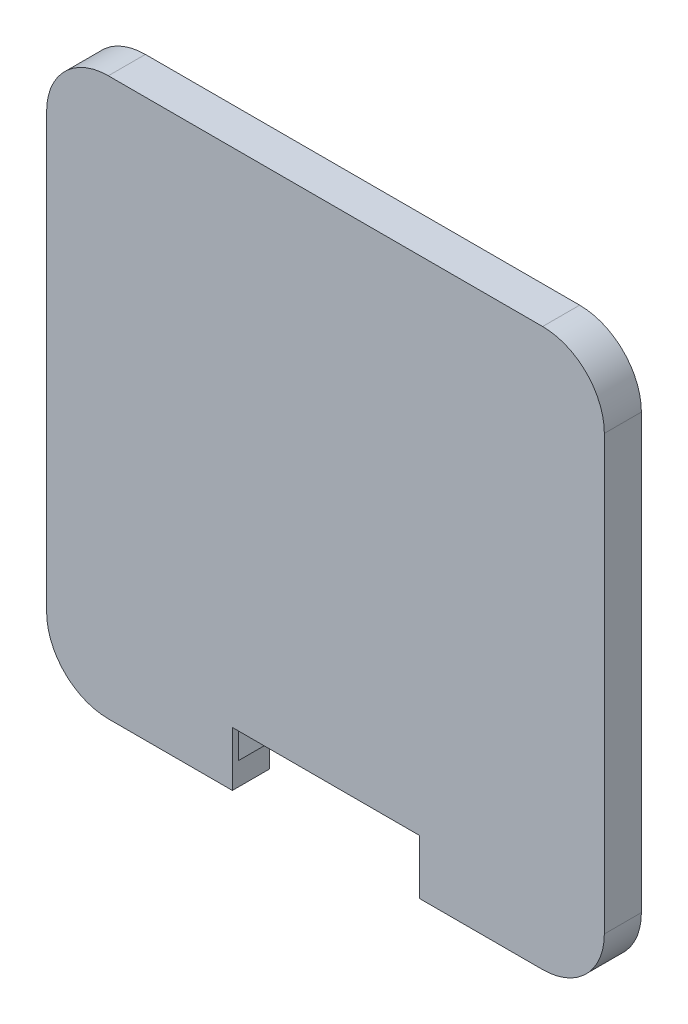
SolidWorks part; units mm, degrees
material "PET"
ref_plane "Front Plane" through (0, 0, 0) normal (0, 0, 1) x (1, 0, 0)
ref_plane "Top Plane" through (0, 0, 0) normal (0, 1, 0) x (1, 0, 0)
ref_plane "Right Plane" through (0, 0, 0) normal (1, 0, 0) x (0, 0, -1)
sketch "Sketch1" plane through (0, 0, 0) normal (0, 0, 1) x (1, 0, 0)
  line L8 (-50.8502, -30.122) -> (-45.1855, -30.122)
  line L9 (15.2147, -41.425) -> (15.2147, -45.122)
  line L10 (-35.1855, -45.122) -> (35.1855, -45.122)
  line L11 (-45.1855, -35.122) -> (-45.1855, 35.122)
  line L12 (-35.1855, 45.122) -> (35.1855, 45.122)
  line L13 (45.1855, -35.122) -> (45.1855, 35.122)
  line L14 (-45.1855, -45.122) -> (45.1855, 45.122) construction
  line L15 (-45.1855, 45.122) -> (45.1855, -45.122) construction
  line L16 (-30.1855, 24.892) -> (-30.1855, -24.892)
  line L17 (-24.9555, -30.122) -> (-19.7221, -30.122)
  line L18 (-19.7221, -30.122) -> (-15.0866, -41.425)
  line L19 (-15.0866, -41.425) -> (15.2147, -41.425)
  line L20 (15.2147, -41.425) -> (19.7232, -30.122)
  line L21 (19.7232, -30.122) -> (24.9555, -30.122)
  line L22 (30.1855, -24.892) -> (30.1855, 24.892)
  line L23 (24.9555, 30.122) -> (-24.9555, 30.122)
  line L24 (-30.1855, 24.892) -> (-30.1855, -24.892)
  line L25 (-24.9555, -30.122) -> (-19.7221, -30.122)
  line L26 (-19.7221, -30.122) -> (-15.0866, -41.425)
  line L27 (-15.0866, -41.425) -> (15.2147, -41.425)
  line L28 (15.2147, -41.425) -> (19.7232, -30.122)
  line L29 (19.7232, -30.122) -> (24.9555, -30.122)
  line L30 (30.1855, -24.892) -> (30.1855, 24.892)
  line L31 (24.9555, 30.122) -> (-24.9555, 30.122)
  line L32 (-15.0866, -41.425) -> (-15.0866, -45.122)
  line L33 (19.7232, -30.122) -> (24.9555, -30.122)
  line L34 (45.1855, -30.122) -> (50.8502, -30.122)
  line L35 (-24.9555, -30.122) -> (-19.7221, -30.122)
  arc A4 (35.1855, -45.122) -> (45.1855, -35.122) centre (35.1855, -35.122) ccw
  arc A5 (-35.1855, -45.122) -> (-45.1855, -35.122) centre (-35.1855, -35.122) cw
  arc A6 (-45.1855, 35.122) -> (-35.1855, 45.122) centre (-35.1855, 35.122) cw
  arc A7 (35.1855, 45.122) -> (45.1855, 35.122) centre (35.1855, 35.122) cw
  arc A8 (-24.9555, 30.122) -> (-30.1855, 24.892) centre (-24.9555, 24.892) ccw
  arc A9 (-30.1855, -24.892) -> (-24.9555, -30.122) centre (-24.9555, -24.892) ccw
  arc A10 (24.9555, -30.122) -> (30.1855, -24.892) centre (24.9555, -24.892) ccw
  arc A11 (30.1855, 24.892) -> (24.9555, 30.122) centre (24.9555, 24.892) ccw
  arc A12 (-24.9555, 30.122) -> (-30.1855, 24.892) centre (-24.9555, 24.892) ccw
  arc A13 (-30.1855, -24.892) -> (-24.9555, -30.122) centre (-24.9555, -24.892) ccw
  arc A14 (24.9555, -30.122) -> (30.1855, -24.892) centre (24.9555, -24.892) ccw
  arc A15 (30.1855, 24.892) -> (24.9555, 30.122) centre (24.9555, 24.892) ccw
  point P0 (0, 0)
  point P3 (0, -30.122)
  dimension "D4" = 10
  dimension "D2" = 15
  dimension "D3" = 15
  dimension "D1" = 0.15
extrude "Boss-Extrude1" add sketch "Sketch1" against normal blind 5 contours A15 L30 A14 L29 L28 L9 L10 A4 L13 A7 L12 A6 L11 A5 L32 L26 L25 A13 L24 A12 L31
sketch "Sketch2" plane through (0, 0, 0) normal (0, 0, 1) x (1, 0, 0)
  line L0 (-45.1855, -35.122) -> (-45.1855, 35.122) construction
  line L1 (-35.1855, -45.122) -> (35.1855, -45.122)
  line L2 (-45.1855, -35.122) -> (-45.1855, 35.122)
  line L3 (-35.1855, 45.122) -> (35.1855, 45.122)
  line L4 (45.1855, -35.122) -> (45.1855, 35.122)
  line L5 (-45.1855, -45.122) -> (45.1855, 45.122) construction
  line L6 (-45.1855, 45.122) -> (45.1855, -45.122) construction
  line L7 (-35.1855, -45.122) -> (-15.0866, -45.122) construction
  line L8 (-14.986, -41.275) -> (15.113, -41.275) construction
  line L9 (-15.0866, -45.122) -> (15.2147, -45.122)
  line L10 (-15.0866, -45.122) -> (-15.0866, -36.275)
  line L11 (-15.0866, -36.275) -> (15.2147, -36.275)
  line L12 (15.2147, -45.122) -> (15.2147, -36.275)
  arc A0 (35.1855, -45.122) -> (45.1855, -35.122) centre (35.1855, -35.122) ccw
  arc A1 (-35.1855, -45.122) -> (-45.1855, -35.122) centre (-35.1855, -35.122) cw
  arc A2 (-45.1855, 35.122) -> (-35.1855, 45.122) centre (-35.1855, 35.122) cw
  arc A3 (35.1855, 45.122) -> (45.1855, 35.122) centre (35.1855, 35.122) cw
  point P0 (0, 0)
  arc M9 (24.9555, 30.122) -> (30.1855, 24.892) centre (24.9555, 24.892) cw
  line M10 (30.1855, 24.892) -> (30.1855, -24.892)
  arc M11 (30.1855, -24.892) -> (24.9555, -30.122) centre (24.9555, -24.892) cw
  line M12 (24.9555, -30.122) -> (19.7232, -30.122)
  line M13 (19.7232, -30.122) -> (15.2147, -41.425)
  line M14 (15.2147, -41.425) -> (15.2147, -45.122)
  line M15 (15.2147, -45.122) -> (35.1855, -45.122)
  arc M16 (35.1855, -45.122) -> (45.1855, -35.122) centre (35.1855, -35.122) ccw
  line M17 (45.1855, -35.122) -> (45.1855, 35.122)
  arc M18 (45.1855, 35.122) -> (35.1855, 45.122) centre (35.1855, 35.122) ccw
  line M19 (35.1855, 45.122) -> (-35.1855, 45.122)
  arc M20 (-35.1855, 45.122) -> (-45.1855, 35.122) centre (-35.1855, 35.122) ccw
  line M21 (-45.1855, 35.122) -> (-45.1855, -35.122)
  arc M22 (-45.1855, -35.122) -> (-35.1855, -45.122) centre (-35.1855, -35.122) ccw
  line M23 (-35.1855, -45.122) -> (-15.0866, -45.122)
  line M24 (-15.0866, -45.122) -> (-15.0866, -41.425)
  line M25 (-15.0866, -41.425) -> (-19.7221, -30.122)
  line M26 (-19.7221, -30.122) -> (-24.9555, -30.122)
  arc M27 (-24.9555, -30.122) -> (-30.1855, -24.892) centre (-24.9555, -24.892) cw
  line M28 (-30.1855, -24.892) -> (-30.1855, 24.892)
  arc M29 (-30.1855, 24.892) -> (-24.9555, 30.122) centre (-24.9555, 24.892) cw
  line M30 (-24.9555, 30.122) -> (24.9555, 30.122)
  dimension "D3" = 10
  dimension "D1" = 0
  dimension "D2" = 0
  dimension "D4" = 5
extrude "Boss-Extrude2" add sketch "Sketch2" along normal blind 1 contours M30 M9 M10 M11 M12 M13 M14 M15 M16 M17 M18 M19 M20 M21 M22 M23 M24 M25 M26 M27 M28 M29 | L12 L10 L11 M13 M12 M11 M10 M9 M30 M29 M28 M27 M26 M25
